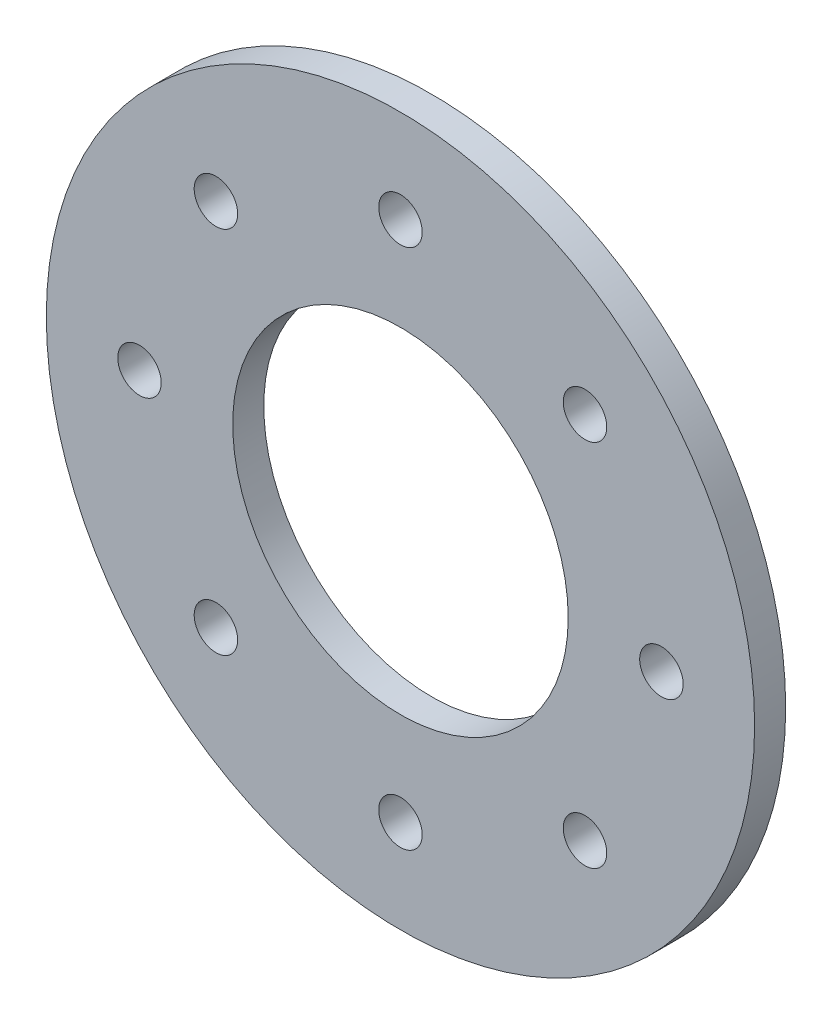
SolidWorks part; units mm, degrees
material "AISI 1045 Steel, cold drawn"
ref_plane "Front Plane" through (0, 0, 0) normal (0, 0, 1) x (1, 0, 0)
ref_plane "Top Plane" through (0, 0, 0) normal (0, 1, 0) x (1, 0, 0)
ref_plane "Right Plane" through (0, 0, 0) normal (1, 0, 0) x (0, 0, -1)
sketch "Sketch3" plane through (0, 0, 0) normal (0, 0, 1) x (1, 0, 0)
  circle A0 centre (0, 0) radius 57
  circle A1 centre (0, 0) radius 27
  circle A3 centre (-42, 0) radius 3.5
  circle A4 centre (-29.6985, 29.6985) radius 3.5
  circle A5 centre (0, 42) radius 3.5
  circle A6 centre (29.6985, 29.6985) radius 3.5
  circle A7 centre (42, 0) radius 3.5
  circle A8 centre (29.6985, -29.6985) radius 3.5
  circle A9 centre (0, -42) radius 3.5
  circle A10 centre (-29.6985, -29.6985) radius 3.5
  point P23 (0, 0)
  dimension "D1" = 114
  dimension "D2" = 54
  dimension "D3" = 42
  dimension "D4" = 7
extrude "Boss-Extrude1" add sketch "Sketch3" along normal blind 5
